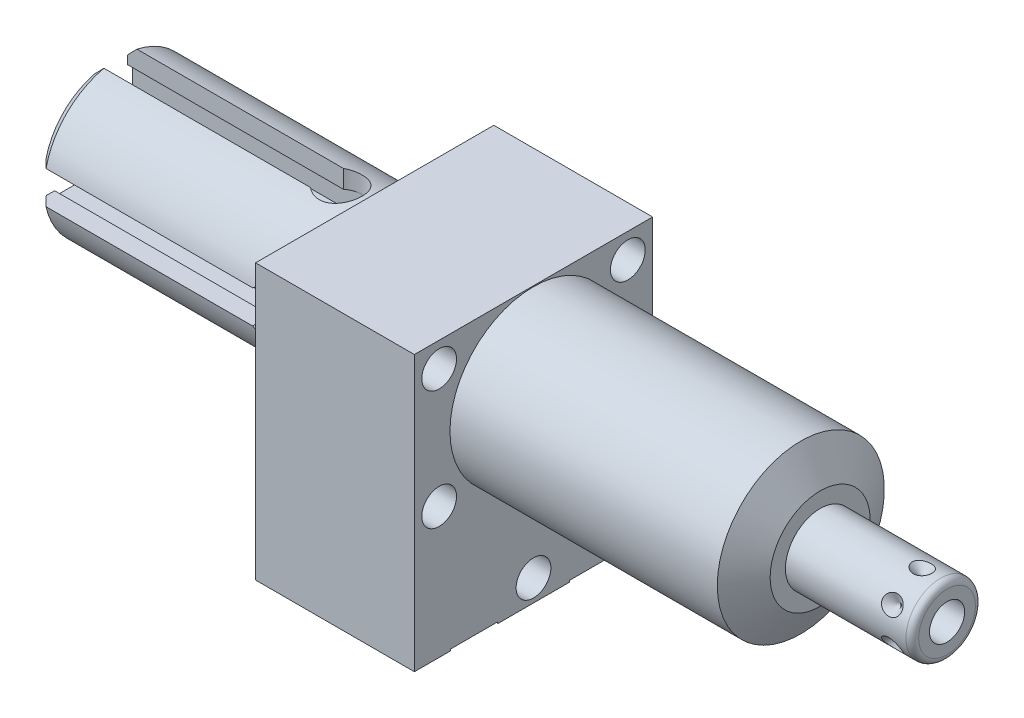
SolidWorks part; units mm, degrees
material "Alloy Steel"
ref_plane "Front Plane" through (0, 0, 0) normal (0, 0, 1) x (1, 0, 0)
ref_plane "Top Plane" through (0, 0, 0) normal (0, 1, 0) x (1, 0, 0)
ref_plane "Right Plane" through (0, 0, 0) normal (1, 0, 0) x (0, 0, -1)
ref_plane "Plane1" through (0, 0, 0) normal (1, 0, 0) x (0, 0, -1)
sketch "Sketch1" plane through (0, 0, 0) normal (1, 0, 0) x (0, 0, -1)
  line L0 (-19.05, 13.4874) -> (-19.05, -30.4546)
  line L1 (-19.05, -30.4546) -> (19.05, -30.4546)
  line L2 (19.05, -30.4546) -> (19.05, 13.4874)
  line L3 (19.05, 13.4874) -> (-19.05, 13.4874)
  line L4 (0, -32.6517) -> (0, 15.6845) construction
  dimension "D1" = 38.1
  dimension "D2" = 43.942
  dimension "D3" = 13.4874
extrude "Extrude1" add sketch "Sketch1" along normal blind 45.847 and the other way blind 25.4
ref_plane "Plane2" through (0, 0, 0) normal (1, 0, 0) x (0, 0, -1)
sketch "Sketch2" plane through (0, 0, 0) normal (1, 0, 0) x (0, 0, -1)
  line L0 (-14.6964, 0) -> (14.6964, 0) construction
  line L5 (19.05, 13.4874) -> (-19.05, 13.4874)
  line L6 (-19.05, 13.4874) -> (-19.05, -30.4546)
  line L7 (-19.05, -30.4546) -> (19.05, -30.4546)
  line L8 (19.05, -30.4546) -> (19.05, 13.4874)
  line L9 (19.05, 13.4874) -> (-19.05, 13.4874)
  line L10 (-19.05, 13.4874) -> (-19.05, -30.4546)
  line L11 (-19.05, -30.4546) -> (19.05, -30.4546)
  line L12 (19.05, -30.4546) -> (19.05, 13.4874)
  circle A0 centre (0, 0) radius 13.3604
  dimension "D1" = 26.7208
  dimension "D2" = 0
extrude "Cut-Extrude1" cut sketch "Sketch2" along normal up to next
ref_plane "Plane3" through (0, 0, 0) normal (0, 0, 1) x (1, 0, 0)
sketch "Sketch3" plane through (0, 0, 0) normal (0, 0, 1) x (1, 0, 0)
  line L0 (42.7527, 13.3604) -> (45.847, 8.001)
  line L1 (42.598, 0) -> (46.0017, 0) construction
  line L2 (45.847, 13.3604) -> (45.847, 8.001)
  line L3 (45.847, 13.3604) -> (42.7527, 13.3604)
  line L4 (45.847, 13.3604) -> (0, 13.3604) construction
  line L5 (45.847, -13.3604) -> (45.847, 13.3604) construction
  dimension "D1" = 30
  dimension "D2" = 16.002
revolve "Cut-Revolve1" cut sketch "Sketch3" angle 360 about L1
ref_plane "Plane4" through (-22.733, -19.8374, 9.525) normal (0, 0, 1) x (0, 1, 0)
sketch "S2D0002" plane through (-22.733, -19.8374, 9.525) normal (0, 0, 1) x (0, 1, 0)
  line L0 (-0.8128, 0) -> (3.7338, 0)
  line L1 (3.7338, 0) -> (3.2938, -2.0701)
  line L2 (3.2938, -2.0701) -> (2.6416, -2.7223)
  line L3 (2.6416, -2.7223) -> (2.6416, -13.97)
  line L4 (2.6416, -13.97) -> (-0.8128, -13.97)
  line L5 (-0.8128, -13.97) -> (-0.8128, 0)
  line L6 (-0.8128, -14.6685) -> (-0.8128, 0.6985) construction
  line L7 (19.8374, -65.4857) -> (19.8374, -22.733) construction
  dimension "D1" = 13.97
  dimension "D2" = 20.6502
revolve "Cut-Revolve2" cut sketch "S2D0002" angle 360 about L6
ref_plane "Plane5" through (-22.733, -19.8374, -9.525) normal (0, 0, 1) x (0, 1, 0)
sketch "Sketch5" plane through (-22.733, -19.8374, -9.525) normal (0, 0, 1) x (0, 1, 0)
  line L0 (-0.8128, 0) -> (3.7338, 0)
  line L1 (3.7338, 0) -> (3.2938, -2.0701)
  line L2 (3.2938, -2.0701) -> (2.6416, -2.7223)
  line L3 (2.6416, -2.7223) -> (2.6416, -13.97)
  line L4 (2.6416, -13.97) -> (-0.8128, -13.97)
  line L5 (-0.8128, -13.97) -> (-0.8128, 0)
  line L6 (-0.8128, -14.6685) -> (-0.8128, 0.6985) construction
  line L7 (19.8374, -65.4857) -> (19.8374, -22.733) construction
  dimension "D1" = 13.97
  dimension "D2" = 20.6502
revolve "Cut-Revolve3" cut sketch "Sketch5" angle 360 about L6
ref_plane "Plane6" through (-8.7376, -30.2006, 9.525) normal (0, 0, 1) x (-1, 0, 0)
sketch "Sketch14" plane through (-25.4, 0, 0) normal (-1, 0, 0) x (0, 0, 1)
  circle A0 centre (-9.525, -20.6502) radius 7.9375
  circle A1 centre (9.525, -20.6502) radius 7.9375
  dimension "D1" = 15.875
extrude "Cut-Extrude2" cut sketch "Sketch14" against normal blind 2.667
sketch "Sketch6" plane through (-8.7376, -30.2006, 9.525) normal (0, 0, 1) x (-1, 0, 0)
  line L0 (16.6624, -43.688) -> (16.6624, 0.254) construction
  line L1 (6.1836, 0) -> (5.641, -2.5527)
  line L2 (5.641, -2.5527) -> (4.9771, -3.2166)
  line L3 (4.9771, -3.2166) -> (4.9771, -17.272)
  line L4 (4.9771, -17.272) -> (0, -17.272)
  line L5 (0, -17.272) -> (0, 0)
  line L6 (0, -18.1356) -> (0, 0.8636) construction
  line L7 (6.1836, 0) -> (9.5237, 0)
  line L8 (9.5237, 0) -> (9.5237, 0.254)
  line L9 (16.6624, 0.254) -> (-8.7376, 0.254) construction
  line L10 (9.5237, 0.254) -> (0, 0.254)
  line L11 (0, 0.254) -> (0, 0)
  dimension "D1" = 19.0475
  dimension "D2" = 0.254
  dimension "D3" = 16.6624
revolve "Cut-Revolve4" cut sketch "Sketch6" angle 360 about L6
ref_plane "Plane7" through (-8.7376, -30.2006, -9.525) normal (0, 0, 1) x (-1, 0, 0)
sketch "Sketch7" plane through (-8.7376, -30.2006, -9.525) normal (0, 0, 1) x (-1, 0, 0)
  line L0 (16.6624, -43.688) -> (16.6624, 0.254) construction
  line L1 (6.1849, 0) -> (5.6423, -2.5527)
  line L2 (5.6423, -2.5527) -> (4.9784, -3.2166)
  line L3 (4.9784, -3.2166) -> (4.9784, -17.272)
  line L4 (4.9784, -17.272) -> (0, -17.272)
  line L5 (0, -17.272) -> (0, 0)
  line L6 (0, -18.1356) -> (0, 0.8636) construction
  line L7 (6.1849, 0) -> (9.5237, 0)
  line L8 (9.5237, 0) -> (-8.7376, 0) construction
  line L9 (9.5237, 0) -> (9.5237, 0.254)
  line L10 (16.6624, 0.254) -> (-8.7376, 0.254) construction
  line L11 (9.5237, 0.254) -> (0, 0.254)
  line L12 (0, 0.254) -> (0, 0)
  dimension "D1" = 16.6624
  dimension "D2" = 9.9568
  dimension "D3" = 19.0475
revolve "Cut-Revolve5" cut sketch "Sketch7" angle 360 about L6
ref_plane "Plane8" through (0, 0, 0) normal (0, 0, 1) x (1, 0, 0)
sketch "Sketch8" plane through (0, 0, 0) normal (0, 0, 1) x (1, 0, 0)
  line L0 (45.847, 0) -> (45.847, 5.5562)
  line L1 (45.847, 5.5562) -> (65.1256, 5.5562)
  line L2 (66.1416, 4.5403) -> (66.1416, 0)
  line L3 (66.1416, 0) -> (45.847, 0)
  line L4 (44.8323, 0) -> (67.1563, 0) construction
  line L5 (45.847, -8.001) -> (45.847, 8.001) construction
  line L6 (-25.4, 13.4874) -> (-25.4, -30.4546) construction
  arc A0 (66.1416, 4.5403) -> (65.1256, 5.5562) centre (65.1256, 4.5403) ccw
  point P0 (45.847, 0)
  dimension "D3" = 1.016
  dimension "D1" = 91.5416
  dimension "D2" = 11.1125
revolve "Revolve1" add sketch "Sketch8" angle 360 about L4
ref_plane "Plane9" through (66.1416, -2.8067, 0) normal (0, 0, 1) x (0, -1, 0)
sketch "S2D0001" plane through (66.1416, -2.8067, 0) normal (0, 0, 1) x (0, -1, 0)
  line L0 (0, 0) -> (0, -10.16)
  line L1 (0, -10.16) -> (-2.8067, -11.8464)
  line L2 (0, 0) -> (-2.8067, 0)
  line L3 (-2.8067, 0) -> (-2.8067, -11.8464)
  line L4 (-2.8067, -12.4388) -> (-2.8067, 0.5923) construction
  line L5 (1.7335, 0) -> (-7.3469, 0) construction
  dimension "D1" = 5.6134
  dimension "D2" = 10.16
  dimension "D3" = 59
revolve "Cut-Revolve6" cut sketch "S2D0001" angle 360 about L4
ref_plane "Plane12" through (62.1792, -5.5562, 0) normal (0, 0, 1) x (-1, 0, 0)
sketch "Sketch12" plane through (62.1792, -5.5562, 0) normal (0, 0, 1) x (-1, 0, 0)
  line L0 (0, 0) -> (1.5875, 0)
  line L1 (1.5875, 0) -> (0, -1.5875)
  line L2 (0, 0) -> (0, -1.5875)
  line L3 (0, -3.434) -> (0, 0.0794) construction
  line L4 (16.3322, 0) -> (-2.9464, 0) construction
  line L5 (-3.9624, -1.016) -> (-3.9624, -10.0965) construction
  dimension "D1" = 3.9624
  dimension "D2" = 45
  dimension "D3" = 3.175
revolve "Cut-Revolve7" cut sketch "Sketch12" angle 360 about L3
pattern_circular "CirPattern1" count 6 over 360 about axis through (45.848, 0, 0) along (-1, 0, 0) of "Cut-Revolve7"
hole_wizard "Hole1" positions "Sketch17" profile "Sketch16" legacy end condition up to next
sketch "Sketch17" plane through (0, 0, 0) normal (1, 0, 0) x (0, 0, -1)
  line L0 (0, 0) -> (0, 17.9298) construction
  line L1 (0, 0) -> (-24.6425, 0) construction
  point P0 (-15.0876, 9.525)
  point P10 (-15.0876, -9.525)
  point P12 (15.0876, 9.525)
  point P13 (15.0876, -9.525)
  point P14 (0, -26.9748)
  dimension "D1" = 9.525
  dimension "D2" = 15.0876
  dimension "D3" = 26.9748
sketch "Sketch16" plane through (0, 9.525, 15.0876) normal (0, 1, 0) x (0, 0, -1)
  line L0 (0, 0) -> (0, 25.4)
  line L1 (0, 25.4) -> (2.7813, 25.4)
  line L2 (2.7813, 25.4) -> (2.7813, 0)
  line L3 (2.7813, 0) -> (0, 0)
  line L4 (0, 110) -> (0, -10) construction
  dimension "Diameter" = 5.5626
  dimension "Depth" = 25.4
sketch "Sketch18" plane through (-8.7376, -30.2006, 9.525) normal (0, 0, 1) x (-1, 0, 0)
  line L0 (-0.6385, -9.5504) -> (23.3703, -9.5504) construction
  line L1 (11.2731, -9.5504) -> (3.5849, -9.5504) construction
  line L3 (13.9954, -17.4879) -> (13.9954, -1.6129) construction
  circle A0 centre (15.7607, -3.3782) radius 1.7653
  dimension "D1" = 3.5306
  dimension "D2" = 12.3444
revolve "Revolve2" add sketch "Sketch18" angle 360 about L0
sketch "Sketch19" plane through (-25.4, 0, 0) normal (-1, 0, 0) x (0, 0, 1)
  circle A0 centre (0, 0) radius 11.3665
  circle A1 centre (0, 0) radius 11.1125
  dimension "D1" = 22.225
  dimension "D2" = 22.733
extrude "Cut-Extrude3" cut sketch "Sketch19" against normal blind 2.921
sketch "Sketch20" plane through (0, 0, 0) normal (0, 0, 1) x (1, 0, 0)
  line L0 (0, 0) -> (-86.9541, 0) construction
  line L1 (-25.4, 11.1125) -> (-26.0604, 11.1125)
  line L2 (-25.4, 13.4874) -> (-25.4, -30.4546) construction
  line L3 (-26.0604, 11.1125) -> (-26.0604, 12.192)
  line L4 (-26.0604, 12.192) -> (-67.5894, 12.192)
  line L5 (-67.5894, 12.192) -> (-67.5894, 0)
  line L6 (-67.5894, 0) -> (-25.4, 0)
  line L7 (-25.4, 0) -> (-25.4, 11.1125)
  line L8 (-22.479, 11.1125) -> (-25.4, 11.1125) construction
  dimension "D1" = 24.384
  dimension "D2" = 41.529
  dimension "D3" = 0.6604
revolve "Revolve3" add sketch "Sketch20" angle 360 about L0
chamfer "Chamfer1" distance 1.524 angle 45 1 edges at (-67.5894, 0, -12.192)
sketch "Sketch21" plane through (-67.5894, 0, 0) normal (-1, 0, 0) x (0, 0, 1)
  line L0 (0, 0) -> (0, 21.975) construction
  line L1 (0, 0) -> (23.3793, 0) construction
  line L2 (11.9024, 2.6416) -> (9.0043, 2.6416)
  line L3 (9.0043, 2.6416) -> (9.0043, 3.429)
  line L4 (9.0043, 3.429) -> (5.7023, 3.429)
  line L5 (5.7023, 3.429) -> (5.7023, -3.429)
  line L6 (11.9024, -2.6416) -> (9.0043, -2.6416)
  line L7 (9.0043, -2.6416) -> (9.0043, -3.429)
  line L8 (9.0043, -3.429) -> (5.7023, -3.429)
  circle A0 centre (0, 0) radius 12.192 construction
  arc A1 (11.9024, -2.6416) -> (11.9024, 2.6416) centre (0, 0) ccw
  dimension "D4" = 6.4897
  dimension "D1" = 5.2832
  dimension "D2" = 6.858
  dimension "D3" = 3.302
extrude "Cut-Extrude4" cut sketch "Sketch21" against normal offset from surface (36.7538 mm away) 4.7752 up to face at (-26.0604, 0, -12.192)
sketch "Sketch22" plane through (0, 0, 5.7023) normal (0, 0, 1) x (1, 0, 0)
  line L0 (-30.8356, 3.429) -> (-30.8356, -3.429) construction
  circle A0 centre (-30.8356, 0) radius 3.429
  dimension "D1" = 6.858
extrude "Cut-Extrude5" cut sketch "Sketch22" along normal through all
pattern_circular "CirPattern2" count 4 over 360 about axis through (0, 0, 0) along (1, 0, 0) of "Cut-Extrude5", "Cut-Extrude4"
